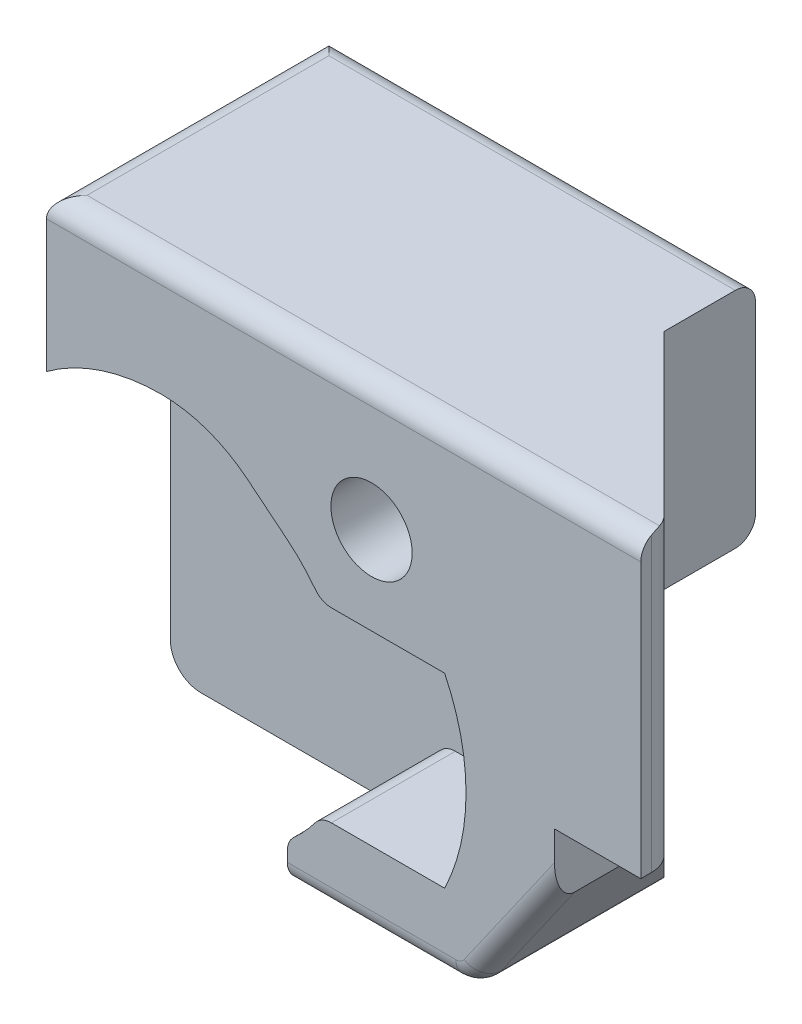
SolidWorks part; units mm, degrees
ref_plane "Front Plane" through (0, 0, 0) normal (0, 0, 1) x (1, 0, 0)
ref_plane "Top Plane" through (0, 0, 0) normal (0, 1, 0) x (1, 0, 0)
ref_plane "Right Plane" through (0, 0, 0) normal (1, 0, 0) x (0, 0, -1)
sketch "Sketch1" plane through (0, 0, 0) normal (0, 0, 1) x (1, 0, 0)
  line L1 (-14.859, 11.938) -> (0, 11.938)
  line L2 (-14.859, 11.938) -> (-14.859, 0)
  line L3 (-14.859, 0) -> (-3.175, 0)
  line L4 (0, 11.938) -> (0, 4.572)
  line L7 (0, 4.572) -> (-3.175, 4.572)
  line L8 (-3.175, 0) -> (-3.175, 4.572)
  dimension "D1" = 11.684
  dimension "D2" = 7.366
  dimension "D3" = 14.859
  dimension "D4" = 11.938
extrude "Extrude1" add sketch "Sketch1" against normal blind 4.7752
sketch "Sketch2" plane through (0, 11.938, 0) normal (0, 1, 0) x (1, 0, 0)
  line L0 (0, 0.5842) -> (-4.191, 4.7752)
  line L1 (0, 4.7752) -> (0, 0) construction
  line L2 (0, 4.7752) -> (-14.859, 4.7752) construction
  line L3 (-4.191, 4.7752) -> (0, 4.7752)
  line L4 (0, 4.7752) -> (0, 0.5842)
  dimension "D1" = 45
  dimension "D2" = 0.5842
extrude "Extrude2" cut sketch "Sketch2" against normal through all
sketch "Sketch33" plane through (-14.859, 0, 0) normal (-1, 0, 0) x (0, 0, 1)
  line L1 (-4.7752, 11.938) -> (-7.0612, 11.938)
  line L2 (-4.7752, 11.938) -> (-4.7752, 6.35)
  line L3 (-4.7752, 6.35) -> (-7.0612, 6.35)
  line L4 (-7.0612, 11.938) -> (-7.0612, 6.35)
  dimension "D1" = 5.588
  dimension "D2" = 2.286
extrude "Extrude30" add sketch "Sketch33" against normal up to vertex (10.668 mm away) up to point (-4.191, 11.938, -4.7752)
sketch "Unlocked" plane through (0, 0, 0) normal (0, 0, 1) x (1, 0, 0)
  circle A0 centre (-9.7028, 4.2418) radius 4.191
  dimension "D3" = 8.382
  dimension "D1" = 2.1082
  dimension "D2" = 5.1562
sketch "End Pressure" plane through (0, 0, 0) normal (0, 0, 1) x (1, 0, 0)
  circle A0 centre (-11.4808, 4.2418) radius 4.191
  dimension "D2" = 8.382
  dimension "D1" = 1.778
sketch "No End Pressure" plane through (0, 0, 0) normal (0, 0, 1) x (1, 0, 0)
  circle A0 centre (-11.9888, 4.2418) radius 4.191
  dimension "D1" = 8.382
  dimension "D2" = 0.508
sketch "Wide Arc" plane through (0, 0, 0) normal (0, 0, 1) x (1, 0, 0)
  circle A10 centre (-11.4808, 4.2418) radius 4.572
  arc A11 (-11.7348, -0.3231) -> (-11.7348, 8.8067) centre (-11.4808, 4.2418) ccw
  circle A13 centre (-11.9888, 4.2418) radius 4.572
  arc A14 (-11.7348, 8.8067) -> (-11.7348, -0.3231) centre (-11.9888, 4.2418) ccw
  dimension "D1" = 0.381
  dimension "D2" = 0.381
sketch "Sketch5" plane through (0, 0, 0) normal (0, 0, 1) x (1, 0, 0)
  line L0 (-14.859, 0) -> (-3.175, 0) construction
  line L1 (-8.962, -0.141) -> (-11.1845, -0.5167) construction
  line L2 (-9.0043, 0.1094) -> (-11.2268, -0.2663) construction
  line L5 (-14.859, 11.938) -> (-14.859, 0) construction
  line L8 (-14.859, 8.1215) -> (-14.859, 0)
  line L9 (-14.859, 0) -> (-8.3742, 0)
  circle A0 centre (-9.7028, 4.2418) radius 4.191 construction
  arc A1 (-9.0043, 0.1094) -> (-8.3436, 8.2063) centre (-9.7028, 4.2418) ccw construction
  arc A2 (-8.3742, 0) -> (-8.2612, 8.4465) centre (-9.7028, 4.2418) ccw
  arc A3 (-8.3436, 8.2063) -> (-11.9888, 8.8138) centre (-11.9888, -2.4257) ccw construction
  arc A4 (-11.7348, 8.8067) -> (-11.7348, -0.3231) centre (-11.9888, 4.2418) ccw construction
  arc A5 (-8.2612, 8.4465) -> (-11.9888, 9.0678) centre (-11.9888, -2.4257) ccw
  arc A6 (-11.9888, 9.0678) -> (-14.859, 8.1215) centre (-11.9888, 4.2418) ccw
  arc A7 (-11.9888, 8.8138) -> (-11.2268, -0.2663) centre (-11.9888, 4.2418) ccw construction
  arc A9 (-8.962, -0.141) -> (-8.2612, 8.4465) centre (-9.7028, 4.2418) ccw construction
  dimension "D1" = 0.254
extrude "Extrude3" cut sketch "Sketch5" against normal blind 3.0988
sketch "Sketch8" plane through (0, 0, 0) normal (0, 0, 1) x (1, 0, 0)
  line L0 (-5.9161, 6.5697) -> (-7.9958, 6.5697)
  line L1 (-8.8371, 7.4938) -> (-8.8371, 8.6017)
  circle A0 centre (-11.4808, 4.2418) radius 4.191 construction
  arc A1 (-7.9958, 6.5697) -> (-8.8371, 7.4938) centre (-11.4808, 4.2418) ccw
  arc A3 (-5.9161, 6.5697) -> (-8.8371, 8.6017) centre (-9.7028, 4.2418) ccw
  arc A5 (-8.3742, 0) -> (-8.2612, 8.4465) centre (-9.7028, 4.2418) ccw construction
  dimension "D1" = 2.921
  dimension "D2" = 2.032
extrude "Extrude6" add sketch "Sketch8" against normal up to surface (3.0988 mm away) up to face at (-11.0666, 5.1959, -3.0988)
sketch "Sketch9" plane through (0, 0, 0) normal (0, 0, 1) x (1, 0, 0)
  line L0 (-5.9161, 1.9139) -> (-7.9958, 1.9139)
  line L1 (-8.8371, 0) -> (-8.8371, 0.9898)
  line L2 (-8.3742, 0) -> (-8.8371, 0)
  line L3 (-8.8371, -0.1181) -> (-8.8371, 0) construction
  arc A0 (-8.3742, 0) -> (-8.8371, -0.1181) centre (-9.7028, 4.2418) cw construction
  circle A1 centre (-11.4808, 4.2418) radius 4.191 construction
  arc A2 (-8.3742, 0) -> (-5.9161, 1.9139) centre (-9.7028, 4.2418) ccw
  arc A3 (-8.8371, 0.9898) -> (-7.9958, 1.9139) centre (-11.4808, 4.2418) ccw
  arc A4 (-8.3742, 0) -> (-5.9161, 6.5697) centre (-9.7028, 4.2418) ccw construction
  dimension "D1" = 2.921
  dimension "D2" = 2.032
extrude "Extrude7" add sketch "Sketch9" against normal up to surface (3.0988 mm away) up to face at (-9.8151, 6.0773, -3.0988)
sketch "Sketch23" plane through (-8.8371, 0, 0) normal (-1, 0, 0) x (0, 0, 1)
  line L0 (-3.0988, 7.4938) -> (-3.0988, 8.6017) construction
  line L1 (0, 7.4938) -> (-3.0988, 7.4938)
  line L2 (0, 7.4938) -> (0, 8.6272)
  line L3 (0, 8.6272) -> (-3.0988, 8.6272)
  line L4 (-3.0988, 7.4938) -> (-3.0988, 8.6272)
  line L7 (-3.0988, 7.4938) -> (0, 7.4938) construction
extrude "Extrude20" add sketch "Sketch23" against normal blind 2.54
sketch "Sketch18" plane through (0, 0, 0) normal (0, 0, 1) x (1, 0, 0)
  line L0 (-4.9036, 6.5697) -> (-5.9161, 6.5697)
  line L1 (-4.9036, 1.9139) -> (-5.9161, 1.9139)
  line L2 (-7.9958, 6.5697) -> (-5.9161, 6.5697) construction
  line L5 (-5.9161, 1.9139) -> (-7.9958, 1.9139) construction
  arc A2 (-4.9036, 1.9139) -> (-4.9036, 6.5697) centre (-9.7028, 4.2418) ccw
  arc A3 (-5.1588, 1.4483) -> (-5.1588, 7.0353) centre (-9.7028, 4.2418) ccw construction
  arc A4 (-5.9161, 1.9139) -> (-5.9161, 6.5697) centre (-9.7028, 4.2418) ccw
  arc A5 (-5.9161, 1.9139) -> (-5.9161, 6.5697) centre (-9.7028, 4.2418) ccw construction
  dimension "D1" = 0.889
extrude "Extrude16" cut sketch "Sketch18" against normal up to surface (3.0988 mm away) up to face at (-9.4738, 4.6916, -3.0988)
fillet "Fillet1" radius 0.762 1 edges at (0, 8.255, -0.5842)
sketch "Sketch24" plane through (0, 0, 0) normal (0, 0, 1) x (1, 0, 0)
  line L0 (-8.8371, 7.4938) -> (-9.8301, 8.3011)
  line L1 (-8.8371, 9.0678) -> (-8.8371, 7.4938)
  line L2 (-8.8371, 8.6272) -> (-8.8371, 7.4938) construction
  line L3 (-8.8371, 9.0678) -> (-11.9888, 9.0678)
  arc A0 (-7.9958, 6.5697) -> (-8.8371, 7.4938) centre (-11.4808, 4.2418) ccw construction
  arc A6 (-9.8301, 8.3011) -> (-11.9888, 9.0678) centre (-11.9888, 5.6457) ccw
  arc A8 (-11.9888, 9.0678) -> (-14.859, 8.1215) centre (-11.9888, 4.2418) ccw construction
extrude "Extrude21" add sketch "Sketch24" against normal up to surface (3.0988 mm away) up to face at (-9.301, 4.6916, -3.0988)
fillet "Fillet2" radius 0.762 1 edges at (-14.859, 0, -3.937)
sketch "Sketch31" plane through (0, 0, 0) normal (0, 0, 1) x (1, 0, 0)
  line L0 (-3.175, 1.4994) -> (-4.2249, 0)
  line L1 (-3.175, 0) -> (-3.175, 4.572) construction
  line L2 (-8.8371, 0) -> (-3.175, 0) construction
  line L3 (-4.2249, 0) -> (-3.175, 0)
  line L4 (-3.175, 0) -> (-3.175, 1.4994)
  line L5 (-3.175, 1.4994) -> (-1.397, 4.0386) construction
  line L7 (-1.397, 4.0386) -> (-1.397, 4.572) construction
  line L8 (-3.175, 4.572) -> (0, 4.572) construction
  dimension "D1" = 55
  dimension "D2" = 1.778
  dimension "D3" = 0.5334
extrude "Extrude28" cut sketch "Sketch31" against normal through all
sketch "Sketch32" plane through (0, 0, 0) normal (0, 0, 1) x (1, 0, 0)
  line L0 (-3.175, 1.4994) -> (-2.159, 2.9504)
  line L1 (-2.159, 2.9504) -> (-2.159, 4.572)
  line L2 (-3.175, 4.572) -> (0, 4.572) construction
  line L3 (-2.159, 4.572) -> (-3.175, 4.572)
  line L4 (-3.175, 4.572) -> (-3.175, 1.4994)
  line L5 (-2.159, 2.9504) -> (-1.0235, 4.572) construction
  line L6 (-3.175, 1.4994) -> (-4.2249, 0) construction
  dimension "D1" = 1.016
extrude "Extrude29" add sketch "Sketch32" against normal up to surface (2.7432 mm away)
fillet "Fillet3" radius 0.762 1 edges at (-4.2249, 0, -2.3876)
fillet "Fillet4" radius 0.508 3 edges at (-3.0782, 1.6376, 0) (-4.2697, 0.0861, 0) (-6.7293, 0, 0)
fillet "Fillet5" radius 0.508 4 edges at (-9.525, 11.938, -7.0612) (-9.525, 6.35, -7.0612) (-7.4295, 11.938, 0) (-14.859, 11.938, -3.5306)
fillet "Fillet6" radius 0.508 3 edges at (-8.8371, 0.9898, -1.5494) (-7.9958, 1.9139, -1.5494) (-7.9958, 6.5697, -1.5494)
sketch "Sketch35" plane through (0, 0, 0) normal (0, 0, 1) x (1, 0, 0)
  line L0 (0, 4.572) -> (0, 11.43) construction
  line L1 (-14.351, 11.938) -> (-0.0386, 11.938) construction
  circle A0 centre (-6.731, 8.763) radius 1.016
  dimension "D1" = 2.032
  dimension "D2" = 6.731
  dimension "D3" = 3.175
extrude "Extrude32" cut sketch "Sketch35" against normal through all
sketch "Sketch36" plane through (0, 0, 0) normal (0, 0, 1) x (1, 0, 0)
  line L9 (-8.8371, 0.508) -> (-8.8371, 0) construction
  line L10 (-8.8371, 0) -> (-4.6215, 0) construction
  line L11 (-8.8371, 0.7565) -> (-8.8371, 0.508)
  line L12 (-8.8371, 0.508) -> (-4.6215, 0.508)
  line L13 (-4.4135, 0.6163) -> (-2.159, 3.836)
  line L14 (-2.159, 3.836) -> (-2.159, 4.572)
  line L15 (-2.159, 4.572) -> (0, 4.572)
  line L16 (0, 4.572) -> (0, 11.43)
  line L17 (0, 11.43) -> (-14.859, 11.43)
  line L18 (-14.859, 11.43) -> (-14.859, 8.1215)
  line L19 (-9.8301, 8.3011) -> (-8.8371, 7.4938)
  line L20 (-7.734, 6.5697) -> (-4.9036, 6.5697)
  line L21 (-4.9036, 1.9139) -> (-7.734, 1.9139)
  line L22 (-8.8371, 0.7565) -> (-8.8371, 0.508)
  line L23 (-8.8371, 0.508) -> (-4.6215, 0.508)
  line L24 (-4.4135, 0.6163) -> (-2.159, 3.836)
  line L25 (-2.159, 3.836) -> (-2.159, 4.572)
  line L26 (-2.159, 4.572) -> (0, 4.572)
  line L27 (0, 4.572) -> (0, 11.43)
  line L28 (0, 11.43) -> (-14.859, 11.43)
  line L29 (-14.859, 11.43) -> (-14.859, 8.1215)
  line L30 (-9.8301, 8.3011) -> (-8.8371, 7.4938)
  line L31 (-7.734, 6.5697) -> (-4.9036, 6.5697)
  line L32 (-4.9036, 1.9139) -> (-7.734, 1.9139)
  line L33 (-4.6215, 0.508) -> (-8.8371, 0.508) construction
  line L34 (-0.0386, 11.938) -> (-14.351, 11.938)
  line L35 (-14.859, 11.43) -> (0, 11.43)
  line L36 (0, 11.43) -> (0, 11.878)
  line L37 (-0.0386, 11.938) -> (-14.351, 11.938)
  line L38 (-14.859, 11.43) -> (0, 11.43)
  line L39 (0, 11.43) -> (0, 11.878)
  line L40 (-2.159, 2.9504) -> (-2.159, 3.836) construction
  line L41 (-2.159, 3.836) -> (-4.4135, 0.6163) construction
  line L42 (-3.9973, 0.3249) -> (-2.159, 2.9504) construction
  line L43 (-8.8371, 0.508) -> (-8.8371, 0)
  line L44 (-8.8371, 0) -> (-4.6215, 0)
  line L45 (-4.6215, 0.508) -> (-8.8371, 0.508)
  line L46 (-2.159, 2.9504) -> (-2.159, 3.836)
  line L47 (-2.159, 3.836) -> (-4.4135, 0.6163)
  line L48 (-3.9973, 0.3249) -> (-2.159, 2.9504)
  arc A3 (-4.6215, 0) -> (-3.9973, 0.3249) centre (-4.6215, 0.762) ccw construction
  arc A4 (-14.351, 11.938) -> (-14.859, 11.43) centre (-14.351, 11.43) ccw
  arc A5 (-14.351, 11.938) -> (-14.859, 11.43) centre (-14.351, 11.43) ccw
  arc A6 (-4.6215, 0.508) -> (-4.4135, 0.6163) centre (-4.6215, 0.762) ccw construction
  arc A7 (-4.6215, 0) -> (-3.9973, 0.3249) centre (-4.6215, 0.762) ccw
  arc A8 (-4.6215, 0.508) -> (-4.4135, 0.6163) centre (-4.6215, 0.762) ccw
  arc A9 (-8.6698, 1.1333) -> (-8.1391, 1.7125) centre (-11.4808, 4.2418) ccw
  arc A10 (-8.6698, 1.1333) -> (-8.8371, 0.7565) centre (-8.3291, 0.7565) ccw
  arc A11 (-4.6215, 0.508) -> (-4.4135, 0.6163) centre (-4.6215, 0.762) ccw
  arc A12 (-11.9888, 9.0678) -> (-14.859, 8.1215) centre (-11.9888, 4.2418) ccw
  arc A13 (-9.8301, 8.3011) -> (-11.9888, 9.0678) centre (-11.9888, 5.6457) ccw
  arc A14 (-8.1391, 6.7711) -> (-8.8371, 7.4938) centre (-11.4808, 4.2418) ccw
  arc A15 (-8.1391, 6.7711) -> (-7.734, 6.5697) centre (-7.734, 7.0777) ccw
  arc A16 (-4.9036, 1.9139) -> (-4.9036, 6.5697) centre (-9.7028, 4.2418) ccw
  arc A17 (-7.734, 1.9139) -> (-8.1391, 1.7125) centre (-7.734, 1.4059) ccw
  arc A18 (-8.6698, 1.1333) -> (-8.1391, 1.7125) centre (-11.4808, 4.2418) ccw
  arc A19 (-8.6698, 1.1333) -> (-8.8371, 0.7565) centre (-8.3291, 0.7565) ccw
  arc A20 (-4.6215, 0.508) -> (-4.4135, 0.6163) centre (-4.6215, 0.762) ccw
  arc A21 (-11.9888, 9.0678) -> (-14.859, 8.1215) centre (-11.9888, 4.2418) ccw
  arc A22 (-9.8301, 8.3011) -> (-11.9888, 9.0678) centre (-11.9888, 5.6457) ccw
  arc A23 (-8.1391, 6.7711) -> (-8.8371, 7.4938) centre (-11.4808, 4.2418) ccw
  arc A24 (-8.1391, 6.7711) -> (-7.734, 6.5697) centre (-7.734, 7.0777) ccw
  arc A25 (-4.9036, 1.9139) -> (-4.9036, 6.5697) centre (-9.7028, 4.2418) ccw
  arc A26 (-7.734, 1.9139) -> (-8.1391, 1.7125) centre (-7.734, 1.4059) ccw
  spline S2 degree 3 poles (2791.7065, -1060.6437) (-2874.9608, 603.1566) (2940.4697, -163.5031) (-2989.9414, -169.8996) knots -101.513121 -101.513121 -101.513121 -101.513121 95.899421 95.899421 95.899421 95.899421 only from (0, 11.878) to (-0.0386, 11.938)
  spline S3 degree 3 poles (0, 11.878) (0, 11.9182) (-0.0119, 11.938) (-0.0386, 11.938) knots 0 0 0 0 1 1 1 1
  dimension "D1" = 0
  dimension "D2" = 0
